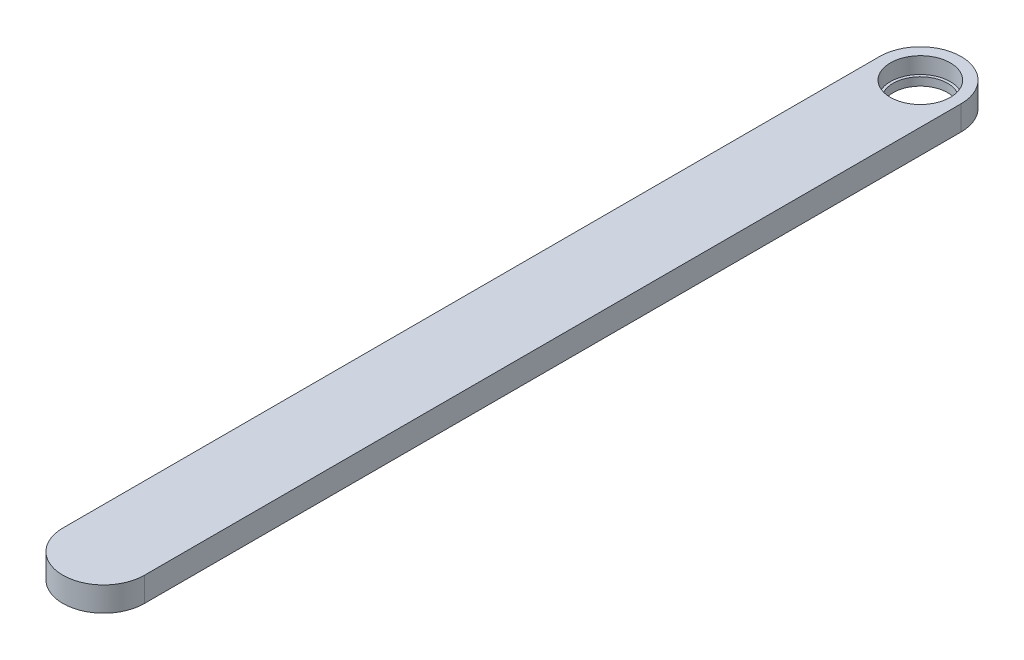
SolidWorks part; units mm, degrees
ref_plane "정면" through (0, 0, 0) normal (0, 0, 1) x (1, 0, 0)
ref_plane "윗면" through (0, 0, 0) normal (0, 1, 0) x (1, 0, 0)
ref_plane "우측면" through (0, 0, 0) normal (1, 0, 0) x (0, 0, -1)
sketch "스케치2" plane through (0, 0, 0) normal (0, 1, 0) x (1, 0, 0)
  line L0 (-15, 0) -> (-15, -300)
  line L1 (0, 0) -> (0, -300) construction
  line L2 (15, 0) -> (15, -300)
  arc A0 (15, 0) -> (-15, 0) centre (0, 0) ccw
  arc A1 (-15, -300) -> (15, -300) centre (0, -300) ccw
  dimension "D1" = 30
  dimension "D3" = 30
  dimension "D2" = 300
extrude "보스-돌출1" add sketch "스케치2" along normal blind 9
sketch "스케치3" plane through (0, 9, 0) normal (0, 1, 0) x (1, 0, 0)
  circle A0 centre (0, 0) radius 11
  dimension "D1" = 22
extrude "컷-돌출1" cut sketch "스케치3" against normal blind 6
sketch "스케치4" plane through (0, 3, 0) normal (0, 1, 0) x (1, 0, 0)
  circle A0 centre (0, 0) radius 10
  dimension "D1" = 20
extrude "컷-돌출2" cut sketch "스케치4" against normal through all
